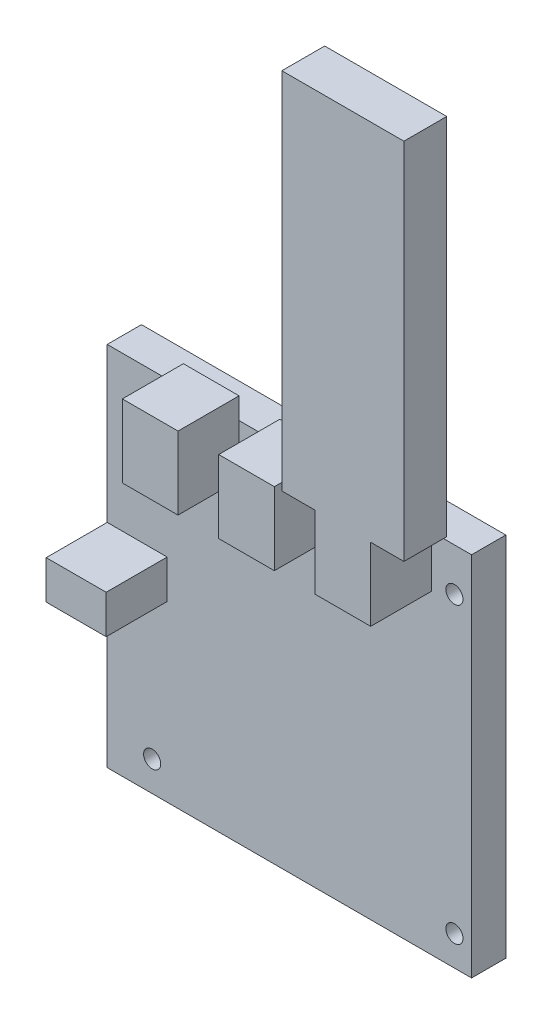
SolidWorks part; units mm, degrees
ref_plane "Front" through (0, 0, 0) normal (0, 0, 1) x (1, 0, 0)
ref_plane "Top" through (0, 0, 0) normal (0, 1, 0) x (1, 0, 0)
ref_plane "Right" through (0, 0, 0) normal (1, 0, 0) x (0, 0, -1)
sketch "Sketch1" plane through (0, 0, 0) normal (0, 0, 1) x (1, 0, 0)
  line L0 (38.545, 32.8) -> (38.545, -35.8) construction
  line L1 (-42.545, -42.8) -> (42.545, -42.8)
  line L2 (-42.545, -42.8) -> (-42.545, 42.8)
  line L3 (-42.545, 42.8) -> (42.545, 42.8)
  line L4 (42.545, -42.8) -> (42.545, 42.8)
  line L5 (-42.545, -42.8) -> (42.545, 42.8) construction
  line L6 (-42.545, 42.8) -> (42.545, -42.8) construction
  line L7 (38.545, -35.8) -> (-32.045, -35.8) construction
  line L8 (-32.045, -35.8) -> (-32.045, 32.8) construction
  line L9 (-32.045, 32.8) -> (38.545, 32.8) construction
  circle A0 centre (-32.045, 32.8) radius 2
  circle A1 centre (38.545, 32.8) radius 2
  circle A2 centre (38.545, -35.8) radius 2
  circle A3 centre (-32.045, -35.8) radius 2
  point P0 (0, 0)
  dimension "D3" = 10
  dimension "D4" = 4
  dimension "D5" = 4
  dimension "D6" = 10.5
  dimension "D7" = 7
  dimension "D1" = 85.09
  dimension "D2" = 85.6
extrude "Boss-Extrude1" add sketch "Sketch1" along normal blind 8
sketch "Sketch2" plane through (0, 0, 8) normal (0, 0, 1) x (1, 0, 0)
  line L0 (38.545, 30.8) -> (-32.045, 30.8) construction
  line L1 (20.245, 30.8) -> (33.245, 30.8)
  line L2 (20.245, 30.8) -> (20.245, 47.8)
  line L3 (20.245, 47.8) -> (33.245, 47.8)
  line L4 (33.245, 30.8) -> (33.245, 47.8)
  line L5 (20.245, 30.8) -> (33.245, 47.8) construction
  line L6 (20.245, 47.8) -> (33.245, 30.8) construction
  line L7 (15.495, 42.8) -> (15.495, 30.8) construction
  line L8 (42.545, 42.8) -> (-42.545, 42.8) construction
  line L9 (10.745, 47.8) -> (-2.255, 30.8) construction
  line L10 (10.745, 30.8) -> (-2.255, 47.8) construction
  line L11 (-2.255, 30.8) -> (-2.255, 47.8)
  line L12 (10.745, 47.8) -> (-2.255, 47.8)
  line L13 (10.745, 30.8) -> (10.745, 47.8)
  line L14 (10.745, 30.8) -> (-2.255, 30.8)
  line L15 (-7.005, 42.8) -> (-7.005, 30.8) construction
  line L16 (-24.755, 30.8) -> (-11.755, 47.8) construction
  line L17 (-24.755, 47.8) -> (-11.755, 30.8) construction
  line L18 (-24.755, 30.8) -> (-11.755, 30.8)
  line L19 (-24.755, 30.8) -> (-24.755, 47.8)
  line L20 (-24.755, 47.8) -> (-11.755, 47.8)
  line L21 (-11.755, 30.8) -> (-11.755, 47.8)
  line L22 (-42.545, 42.8) -> (-42.545, -42.8) construction
  line L23 (-42.545, 6.8) -> (-28.545, 6.8)
  line L24 (-42.545, 6.8) -> (-42.545, -2.2)
  line L25 (-42.545, -2.2) -> (-28.545, -2.2)
  line L26 (-28.545, 6.8) -> (-28.545, -2.2)
  circle A0 centre (38.545, 32.8) radius 2 construction
  circle A2 centre (-32.045, 32.8) radius 2 construction
  point P0 (26.745, 39.3)
  point P19 (4.245, 39.3)
  point P26 (-18.255, 39.3)
  dimension "D1" = 5.3
  dimension "D2" = 13
  dimension "D3" = 17
  dimension "D4" = 4.75
  dimension "D5" = 4.75
  dimension "D6" = 36
  dimension "D7" = 9
  dimension "D8" = 14
extrude "Boss-Extrude2" add sketch "Sketch2" along normal blind 14.25
sketch "Sketch3" plane through (-42.545, 0, 0) normal (-1, 0, 0) x (0, 0, 1)
  line L0 (22.25, 6.8) -> (22.25, -2.2) construction
  line L1 (22.25, 6.8) -> (8, 6.8) construction
  circle A0 centre (16.25, 2.3) radius 2.5
  dimension "D1" = 5
  dimension "D2" = 6
  dimension "D3" = 4.5
extrude "Cut-Extrude1" cut sketch "Sketch3" against normal blind 3
sketch "Sketch4" plane through (0, 47.8, 0) normal (0, 1, 0) x (1, 0, 0)
  line L0 (26.745, -8) -> (26.745, -22.25) construction
  line L1 (12.495, -12.25) -> (40.995, -12.25)
  line L2 (12.495, -12.25) -> (12.495, -22.25)
  line L3 (12.495, -22.25) -> (40.995, -22.25)
  line L4 (40.995, -12.25) -> (40.995, -22.25)
  line L5 (12.495, -12.25) -> (40.995, -22.25) construction
  line L6 (12.495, -22.25) -> (40.995, -12.25) construction
  line L7 (33.245, -8) -> (20.245, -8) construction
  line L8 (33.245, -22.25) -> (20.245, -22.25) construction
  point P0 (26.745, -17.25)
  dimension "D1" = 10
  dimension "D2" = 28.5
extrude "Boss-Extrude3" add sketch "Sketch4" along normal blind 85
